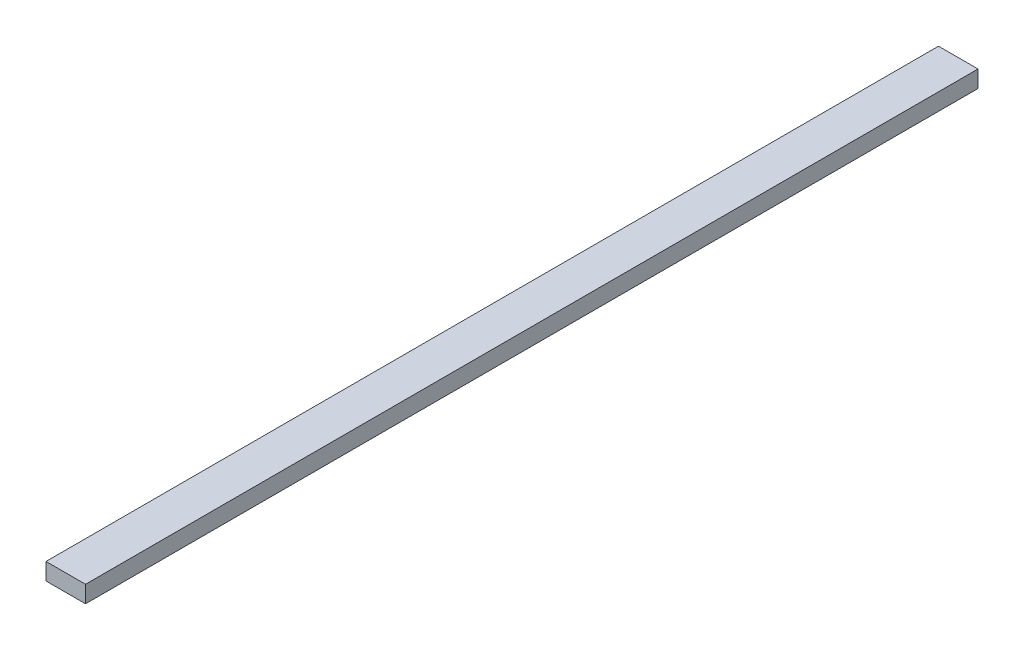
SolidWorks part; units mm, degrees
material "Pine"
ref_plane "Front Plane" through (0, 0, 0) normal (0, 0, 1) x (1, 0, 0)
ref_plane "Top Plane" through (0, 0, 0) normal (0, 1, 0) x (1, 0, 0)
ref_plane "Right Plane" through (0, 0, 0) normal (1, 0, 0) x (0, 0, -1)
sketch "Sketch1" plane through (0, 0, 0) normal (0, 0, 1) x (1, 0, 0)
  line L1 (44.45, 0) -> (44.45, -38.1)
  line L2 (44.45, -38.1) -> (-44.45, -38.1)
  line L3 (-44.45, -38.1) -> (-44.45, 0)
  line L4 (-44.45, 0) -> (44.45, 0)
  dimension "D1" = 38.1
  dimension "D2" = 88.9
extrude "Boss-Extrude1" add sketch "Sketch1" along normal mid plane 2007.9375
equation "\"absorber_plate_width\" = 1100mm"
equation "\"absorber_plate_length\" = 2100mm"
equation "\"absorber_plate_thickness\" = .1875in"
equation "\"groove_depth\" = 20mm"
equation "\"frame_thickness\" = 60mm"
equation "\"insulation_thickness\" = 50mm"
equation "\"glass_thickness\" = 3mm"
equation "\"pipe_distances\" = 100mm"
equation "\"pipe_OD\" = 0.3125in"
equation "\"pipe_ID\" = 0.249in"
equation "\"pipe_straight_length\" = 900mm"
equation "\"absorber_to_glass\" = 25mm"
equation "\"serpentine_length\" = 1900mm"
equation "\"wood_width\" = 3.5in"
equation "\"wood_height\" = 1.5in"
equation "\"D2@Sketch1\"=\"wood_width\""
equation "\"D1@Boss-Extrude1\"=\"serpentine_length\"+\"pipe_OD\"+\"insulation_thickness\"*2"
